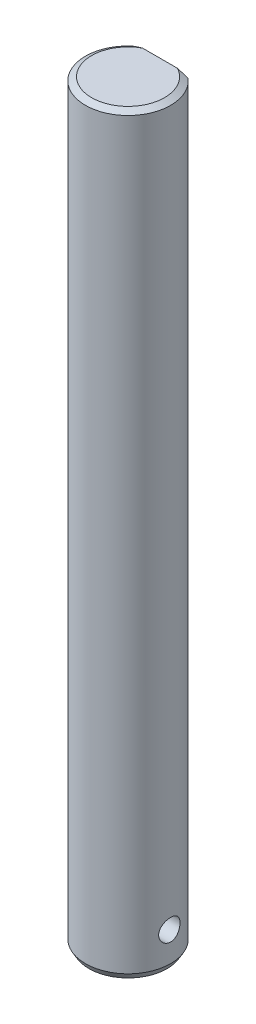
SolidWorks part; units mm, degrees
ref_plane "Front Plane" through (0, 0, 0) normal (0, 0, 1) x (1, 0, 0)
ref_plane "Top Plane" through (0, 0, 0) normal (0, 1, 0) x (1, 0, 0)
ref_plane "Right Plane" through (0, 0, 0) normal (1, 0, 0) x (0, 0, -1)
sketch "Sketch1" plane through (0, 0, 0) normal (0, 1, 0) x (1, 0, 0)
  circle A0 centre (0, 0) radius 6
  dimension "D1" = 12
extrude "Boss-Extrude1" add sketch "Sketch1" along normal blind 106
sketch "Sketch2" plane through (0, 106, 0) normal (0, 1, 0) x (1, 0, 0)
  line L1 (-6.4202, 8.5904) -> (7.5063, 8.5904)
  line L2 (-6.4202, 8.5904) -> (-6.4202, 4.5)
  line L3 (-6.4202, 4.5) -> (7.5063, 4.5)
  line L4 (7.5063, 8.5904) -> (7.5063, 4.5)
  dimension "D1" = 4.5
extrude "Cut-Extrude1" cut sketch "Sketch2" against normal blind 10
sketch "Sketch3" plane through (0, 0, 0) normal (1, 0, 0) x (0, 0, -1)
  line L0 (-6, 0) -> (6, 0) construction
  circle A0 centre (0, 5) radius 1.5
  point P2 (0, 0)
  dimension "D1" = 3
  dimension "D2" = 5
extrude "Cut-Extrude2" cut sketch "Sketch3" against normal mid plane 20
chamfer "Chamfer1" distance 0.5 angle 60 2 edges at (0, 106, 6) (0, 0, 6)
